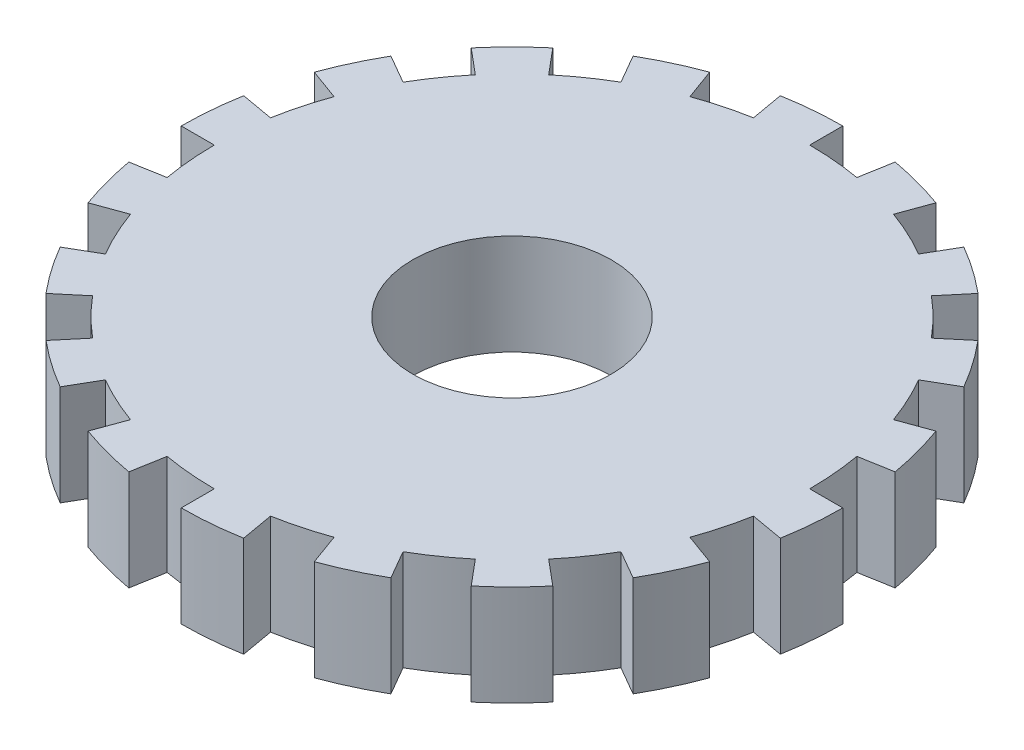
SolidWorks part; units mm, degrees
material "Nylon 6/10"
ref_plane "Front Plane" through (0, 0, 0) normal (0, 0, 1) x (1, 0, 0)
ref_plane "Top Plane" through (0, 0, 0) normal (0, 1, 0) x (1, 0, 0)
ref_plane "Right Plane" through (0, 0, 0) normal (1, 0, 0) x (0, 0, -1)
sketch "Sketch1" plane through (0, 0, 0) normal (0, 1, 0) x (1, 0, 0)
  circle A0 centre (0, 0) radius 31.75
  circle A1 centre (0, 0) radius 9.525
  dimension "D1" = 63.5
  dimension "D2" = 19.05
extrude "Boss-Extrude1" add sketch "Sketch1" along normal blind 9.652
sketch "Sketch2" plane through (0, 9.652, 0) normal (0, 1, 0) x (1, 0, 0)
  line L0 (28.575, 0) -> (43.7827, 0)
  line L1 (28.1409, 4.962) -> (43.7827, 7.7201)
  line L2 (43.7827, 7.7201) -> (43.7827, 0)
  line L3 (28.1409, -4.962) -> (43.7827, -7.7201)
  line L4 (43.7827, -7.7201) -> (41.1423, -14.9746)
  line L5 (26.8517, -9.7732) -> (41.1423, -14.9746)
  line L6 (24.7467, -14.2875) -> (38.5019, -22.2291)
  line L7 (38.5019, -22.2291) -> (33.5395, -28.143)
  line L8 (21.8897, -18.3677) -> (33.5395, -28.143)
  line L9 (18.3677, -21.8897) -> (28.5771, -34.0569)
  line L10 (28.5771, -34.0569) -> (21.8913, -37.9169)
  line L11 (14.2875, -24.7467) -> (21.8913, -37.9169)
  line L12 (9.7732, -26.8517) -> (15.2056, -41.777)
  line L13 (15.2056, -41.777) -> (7.6028, -43.1175)
  line L14 (4.962, -28.1409) -> (7.6028, -43.1175)
  line L15 (0, -28.575) -> (0, -44.4581)
  line L16 (0, -44.4581) -> (-7.6028, -43.1175)
  line L17 (-4.962, -28.1409) -> (-7.6028, -43.1175)
  line L18 (-9.7732, -26.8517) -> (-15.2056, -41.777)
  line L19 (-15.2056, -41.777) -> (-21.8913, -37.9169)
  line L20 (-14.2875, -24.7467) -> (-21.8913, -37.9169)
  line L21 (-18.3677, -21.8897) -> (-28.5771, -34.0569)
  line L22 (-28.5771, -34.0569) -> (-33.5395, -28.143)
  line L23 (-21.8897, -18.3677) -> (-33.5395, -28.143)
  line L24 (-24.7467, -14.2875) -> (-38.5019, -22.2291)
  line L25 (-38.5019, -22.2291) -> (-41.1423, -14.9746)
  line L26 (-26.8517, -9.7732) -> (-41.1423, -14.9746)
  line L27 (-28.1409, -4.962) -> (-43.7827, -7.7201)
  line L28 (-43.7827, -7.7201) -> (-43.7827, 0)
  line L29 (-28.575, 0) -> (-43.7827, 0)
  line L30 (-28.1409, 4.962) -> (-43.7827, 7.7201)
  line L31 (-43.7827, 7.7201) -> (-41.1423, 14.9746)
  line L32 (-26.8517, 9.7732) -> (-41.1423, 14.9746)
  line L33 (-24.7467, 14.2875) -> (-38.5019, 22.2291)
  line L34 (-38.5019, 22.2291) -> (-33.5395, 28.143)
  line L35 (-21.8897, 18.3677) -> (-33.5395, 28.143)
  line L36 (-18.3677, 21.8897) -> (-28.5771, 34.0569)
  line L37 (-28.5771, 34.0569) -> (-21.8913, 37.9169)
  line L38 (-14.2875, 24.7467) -> (-21.8913, 37.9169)
  line L39 (-9.7732, 26.8517) -> (-15.2056, 41.777)
  line L40 (-15.2056, 41.777) -> (-7.6028, 43.1175)
  line L41 (-4.962, 28.1409) -> (-7.6028, 43.1175)
  line L42 (0, 28.575) -> (0, 44.4581)
  line L43 (0, 44.4581) -> (7.6028, 43.1175)
  line L44 (4.962, 28.1409) -> (7.6028, 43.1175)
  line L45 (9.7732, 26.8517) -> (15.2056, 41.777)
  line L46 (15.2056, 41.777) -> (21.8913, 37.9169)
  line L47 (14.2875, 24.7467) -> (21.8913, 37.9169)
  line L48 (18.3677, 21.8897) -> (28.5771, 34.0569)
  line L49 (28.5771, 34.0569) -> (33.5395, 28.143)
  line L50 (21.8897, 18.3677) -> (33.5395, 28.143)
  line L51 (24.7467, 14.2875) -> (38.5019, 22.2291)
  line L52 (38.5019, 22.2291) -> (41.1423, 14.9746)
  line L53 (26.8517, 9.7732) -> (41.1423, 14.9746)
  arc A0 (28.575, 0) -> (28.1409, 4.962) centre (0, 0) ccw
  arc A1 (26.8517, -9.7732) -> (28.1409, -4.962) centre (0, 0) ccw
  arc A2 (21.8897, -18.3677) -> (24.7467, -14.2875) centre (0, 0) ccw
  arc A3 (14.2875, -24.7467) -> (18.3677, -21.8897) centre (0, 0) ccw
  arc A4 (4.962, -28.1409) -> (9.7732, -26.8517) centre (0, 0) ccw
  arc A5 (-4.962, -28.1409) -> (0, -28.575) centre (0, 0) ccw
  arc A6 (-14.2875, -24.7467) -> (-9.7732, -26.8517) centre (0, 0) ccw
  arc A7 (-21.8897, -18.3677) -> (-18.3677, -21.8897) centre (0, 0) ccw
  arc A8 (-26.8517, -9.7732) -> (-24.7467, -14.2875) centre (0, 0) ccw
  arc A9 (-28.575, 0) -> (-28.1409, -4.962) centre (0, 0) ccw
  arc A10 (-26.8517, 9.7732) -> (-28.1409, 4.962) centre (0, 0) ccw
  arc A11 (-21.8897, 18.3677) -> (-24.7467, 14.2875) centre (0, 0) ccw
  arc A12 (-14.2875, 24.7467) -> (-18.3677, 21.8897) centre (0, 0) ccw
  arc A13 (-4.962, 28.1409) -> (-9.7732, 26.8517) centre (0, 0) ccw
  arc A14 (4.962, 28.1409) -> (0, 28.575) centre (0, 0) ccw
  arc A15 (14.2875, 24.7467) -> (9.7732, 26.8517) centre (0, 0) ccw
  arc A16 (21.8897, 18.3677) -> (18.3677, 21.8897) centre (0, 0) ccw
  arc A17 (26.8517, 9.7732) -> (24.7467, 14.2875) centre (0, 0) ccw
  point P77 (0, 0)
  dimension "D1" = 18
  dimension "D2" = 10
  dimension "D3" = 7.7201
extrude "Cut-Extrude1" cut sketch "Sketch2" against normal through all
